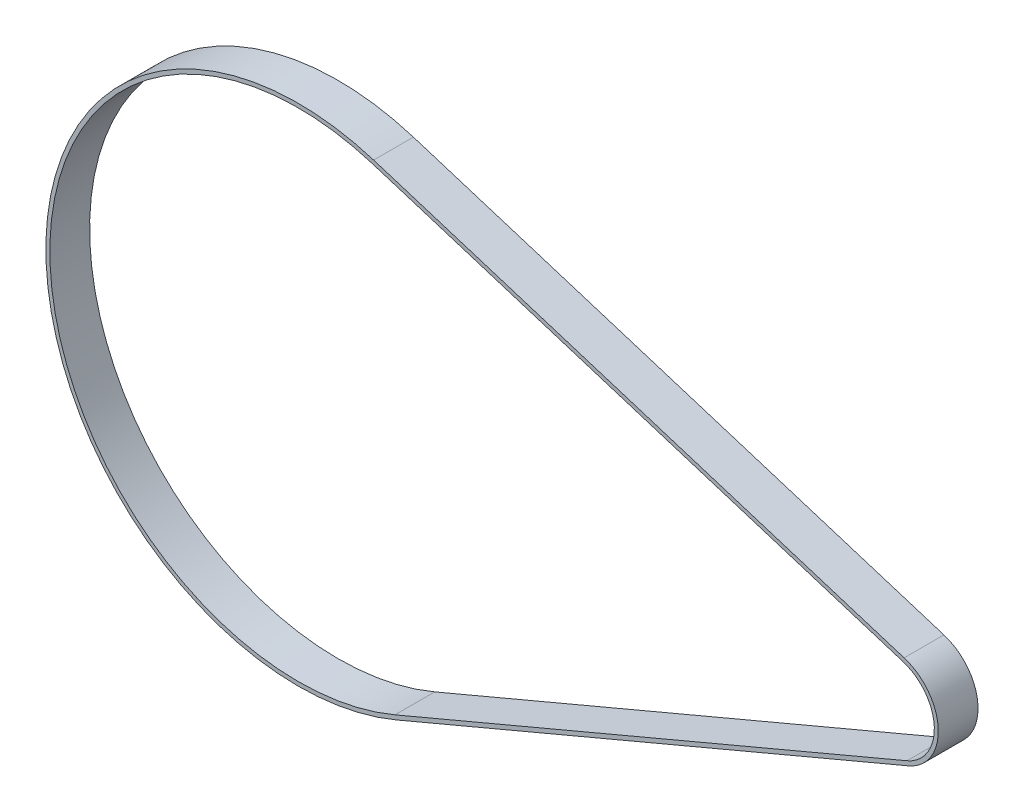
SolidWorks part; units mm, degrees
ref_plane "Front Plane" through (0, 0, 0) normal (0, 0, 1) x (1, 0, 0)
ref_plane "Top Plane" through (0, 0, 0) normal (0, 1, 0) x (1, 0, 0)
ref_plane "Right Plane" through (0, 0, 0) normal (1, 0, 0) x (0, 0, -1)
sketch "Sketch2" plane through (0, 0, 0) normal (0, 0, 1) x (1, 0, 0)
  line L0 (0, 0) -> (1, 0) construction
  line L1 (0, 0) -> (0, 1) construction
  line L2 (37.2991, 119.3054) -> (304.2138, 35.8584)
  line L3 (306.2542, -6.3437) -> (48.6345, -115.1507)
  arc A0 (48.6345, -115.1507) -> (37.2991, 119.3054) centre (0, 0) cw
  arc A1 (304.2138, 35.8584) -> (306.2542, -6.3437) centre (297.5, 14.3834) cw
extrude "Extrude-Thin1" add sketch "Sketch2" along normal mid plane 20 thin thin type one direction wall 2
